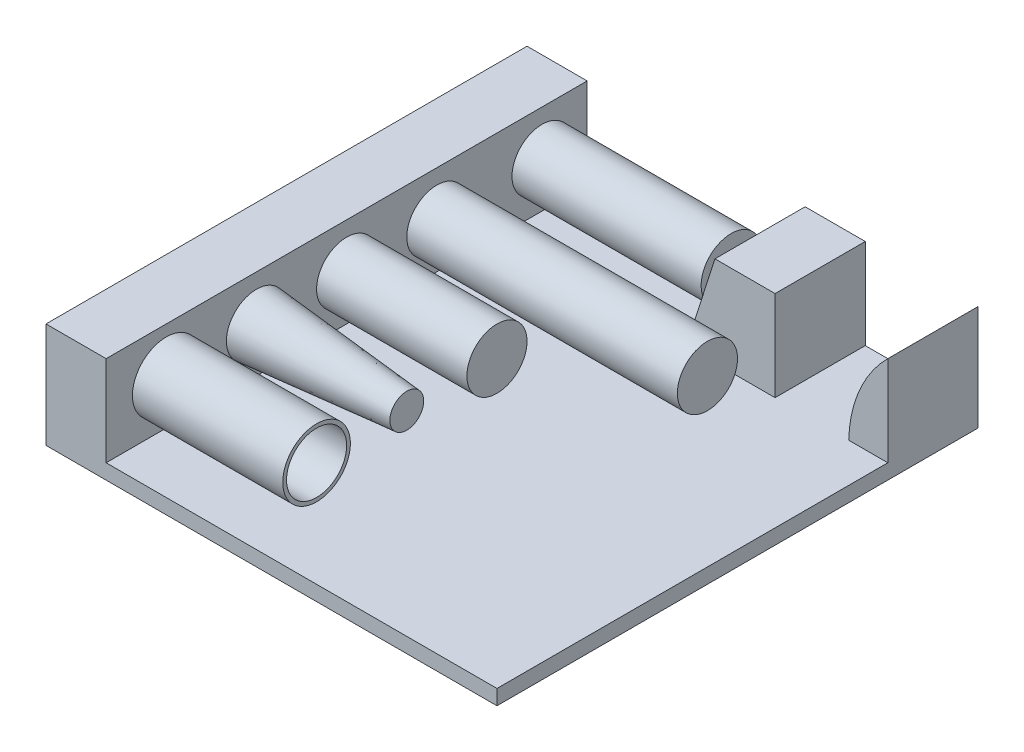
SolidWorks part; units mm, degrees
ref_plane "Front Plane" through (0, 0, 0) normal (0, 0, 1) x (1, 0, 0)
ref_plane "Top Plane" through (0, 0, 0) normal (0, 1, 0) x (1, 0, 0)
ref_plane "Right Plane" through (0, 0, 0) normal (1, 0, 0) x (0, 0, -1)
sketch "Sketch1" plane through (0, 0, 0) normal (0, 0, 1) x (1, 0, 0)
  line L0 (-300, 0) -> (300, 0)
  line L1 (55, 0) -> (-55, 0) construction
  line L2 (-300, 0) -> (-300, 140)
  line L3 (-300, 140) -> (-220, 140)
  line L4 (-220, 140) -> (-220, 20)
  line L5 (0, -55) -> (0, 55) construction
  line L6 (-220, 20) -> (300, 20)
  line L7 (300, 20) -> (300, 0)
  dimension "D1" = 600
  dimension "D2" = 80
  dimension "D3" = 300
  dimension "D4" = 220
  dimension "D5" = 20
  dimension "D6" = 140
extrude "Boss-Extrude1" add sketch "Sketch1" along normal blind 640
sketch "Sketch2" plane through (0, 0, 0) normal (0, 0, 1) x (1, 0, 0)
  line L0 (-220, 140) -> (323.1378, 140) construction
  line L1 (300, 20) -> (300, 140) construction
  line L6 (300, 20) -> (-220, 20) construction
  line L7 (300, 140) -> (300, 20)
  line L8 (300, 20) -> (247.9563, 20)
  line L9 (70, 140) -> (30, 15) construction
  line L11 (150, -14.017) -> (150, 140) construction
  line L12 (150, 140) -> (70, 140)
  line L13 (-220, 20) -> (-220, 140) construction
  line L14 (150, 140) -> (150, 20)
  line L15 (150, 20) -> (31.6, 20)
  line L16 (31.6, 20) -> (70, 140)
  arc A0 (300, 140) -> (247.9563, 20) centre (423.8522, 15) ccw
  point P8 (247.9563, 20)
  point P14 (150, 20)
  point P18 (31.6, 20)
  point P19 (150, 62.9915)
  dimension "D1" = 290
  dimension "D2" = 250
  dimension "D3" = 150
extrude "Boss-Extrude2" add sketch "Sketch2" along normal blind 120
sketch "One_Side" plane through (-220, 0, 0) normal (1, 0, 0) x (0, 0, -1)
  circle A0 centre (-60, 80) radius 40
ref_plane "Plane1" through (-60, 0, 0) normal (1, 0, 0) x (0, 0, -1)
sketch "Both_Sides" plane through (-60, 0, 0) normal (1, 0, 0) x (0, 0, -1)
  circle A0 centre (-200, 80) radius 40
sketch "Solid" plane through (-220, 0, 0) normal (1, 0, 0) x (0, 0, -1)
  circle A0 centre (-320, 80) radius 40
sketch "Thicken" plane through (-220, 0, 0) normal (1, 0, 0) x (0, 0, -1)
  circle A1 centre (-560, 80) radius 40
sketch "Draft" plane through (-220, 0, 0) normal (1, 0, 0) x (0, 0, -1)
  circle A0 centre (-440, 80) radius 40
extrude "Boss-Extrude4" add sketch "One_Side" along normal up to vertex (480.3305 mm away)
extrude "Boss-Extrude5" add sketch "Both_Sides" along normal blind 200 and the other way up to next
extrude "Boss-Extrude6" add sketch "Solid" along normal blind 200
extrude "Boss-Extrude7" add sketch "Draft" along normal blind 200 draft 5
extrude "Extrude-Thin1" add sketch "Thicken" along normal blind 200 thin
